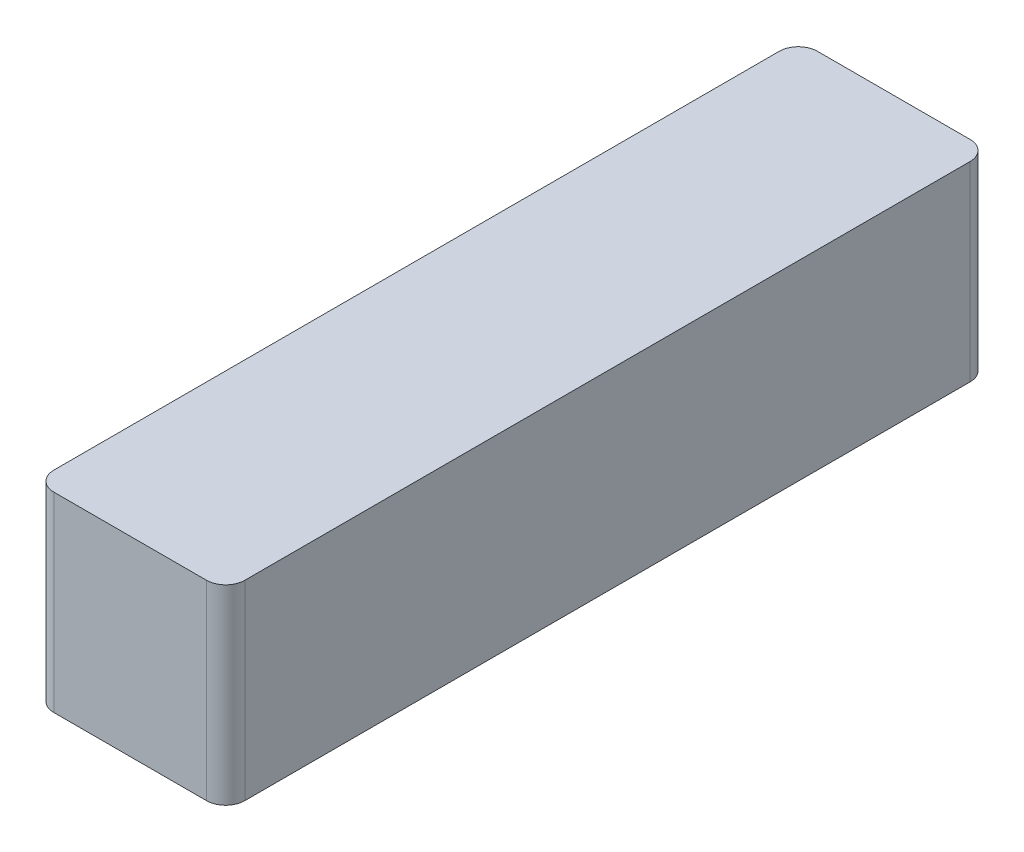
SolidWorks part; units mm, degrees
ref_plane "Front Plane" through (0, 0, 0) normal (0, 0, 1) x (1, 0, 0)
ref_plane "Top Plane" through (0, 0, 0) normal (0, 1, 0) x (1, 0, 0)
ref_plane "Right Plane" through (0, 0, 0) normal (1, 0, 0) x (0, 0, -1)
sketch "Sketch1" plane through (0, 0, 0) normal (0, 1, 0) x (1, 0, 0)
  line L1 (0, 0) -> (10, 0)
  line L2 (0, 0) -> (0, 40)
  line L3 (0, 40) -> (10, 40)
  line L4 (10, 0) -> (10, 40)
  dimension "D1" = 40
  dimension "D2" = 10
extrude "Boss-Extrude1" add sketch "Sketch1" along normal blind 10
fillet "Fillet1" radius 1 4 edges at (10, 5, -40) (0, 5, -40) (10, 5, 0) (0, 5, 0)
